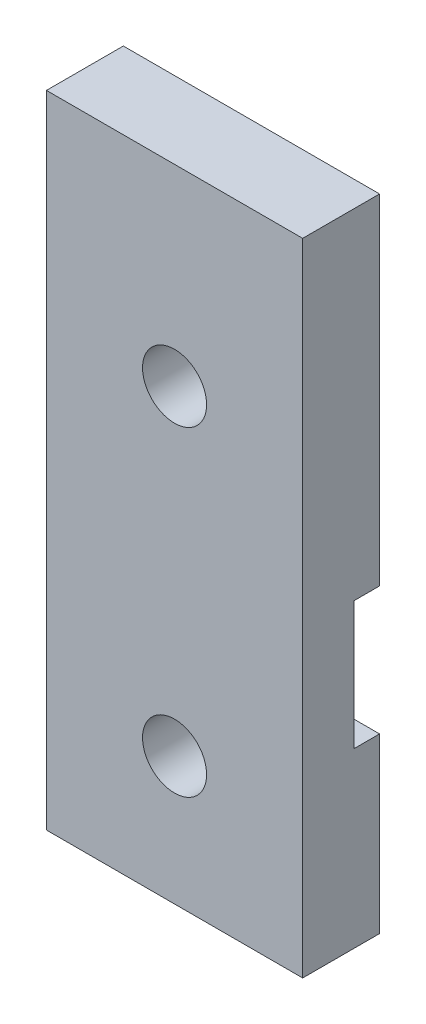
SolidWorks part; units mm, degrees
material "Policarbonato"
ref_plane "Plano frontal" through (0, 0, 0) normal (0, 0, 1) x (1, 0, 0)
ref_plane "Plano superior" through (0, 0, 0) normal (0, 1, 0) x (1, 0, 0)
ref_plane "Plano direito" through (0, 0, 0) normal (1, 0, 0) x (0, 0, -1)
sketch "Esboço1" plane through (0, 0, 0) normal (0, 0, 1) x (1, 0, 0)
  line L1 (0, 0) -> (20, 0)
  line L2 (0, 0) -> (0, 50)
  line L3 (0, 50) -> (20, 50)
  line L4 (20, 0) -> (20, 50)
  dimension "D1" = 20
  dimension "D2" = 50
extrude "Ressalto-extrusão1" add sketch "Esboço1" along normal blind 6
sketch "Esboço2" plane through (0, 0, 0) normal (0, 0, -1) x (-1, 0, 0)
  line L0 (-10, 35) -> (-10, 10) construction
  line L4 (0, 0) -> (0, 50)
  line L5 (0, 50) -> (-20, 50)
  line L6 (-20, 50) -> (-20, 0)
  line L7 (-20, 0) -> (0, 0)
  line L8 (0, 0) -> (0, 50)
  line L9 (0, 50) -> (-20, 50)
  line L10 (-20, 50) -> (-20, 0)
  line L11 (-20, 0) -> (0, 0)
  circle A0 centre (-10, 35) radius 2.5 construction
  circle A1 centre (-10, 35) radius 2.5
  circle A3 centre (-3.25, 18.5) radius 2.5 construction
  circle A5 centre (-3.25, 18.5) radius 2.5
  circle A6 centre (-10, 10) radius 2.5
  dimension "D2" = 10
  dimension "D1" = 0
extrude "Corte-extrusão1" cut sketch "Esboço2" against normal blind 10
sketch "Esboço3" plane through (0, 0, 0) normal (0, 0, 1) x (1, 0, 0)
  line L0 (10, 50) -> (10, 41.4324) construction
  line L1 (20, 50) -> (0, 50) construction
  circle A0 centre (3.25, 18.5) radius 5
  circle A1 centre (16.75, 18.5) radius 5
  dimension "D1" = 10
extrude "Corte-extrusão2" cut sketch "Esboço3" along normal blind 2
sketch "Esboço4" plane through (0, 0, 0) normal (0, 0, -1) x (-1, 0, 0)
  line L0 (-3.25, 23.5) -> (0, 23.5)
  line L1 (0, 50) -> (0, 22.2997) construction
  line L2 (0, 23.5) -> (0, 13.5)
  line L3 (0, 14.7003) -> (0, 0) construction
  line L4 (0, 13.5) -> (-3.25, 13.5)
  line L5 (-3.25, 13.5) -> (-3.25, 23.5)
  line L6 (-10, 50) -> (-10, 41.2912) construction
  line L7 (-20, 50) -> (0, 50) construction
  line L8 (-20, 13.5) -> (-16.75, 13.5)
  line L9 (-20, 23.5) -> (-20, 13.5)
  line L10 (-16.75, 23.5) -> (-20, 23.5)
  line L11 (-16.75, 13.5) -> (-16.75, 23.5)
  arc A0 (0, 22.2997) -> (0, 14.7003) centre (-3.25, 18.5) ccw construction
  arc A1 (0, 22.2997) -> (0, 14.7003) centre (-3.25, 18.5) ccw construction
  point P10 (-3.25, 18.5)
  point P15 (-3.25, 23.5)
extrude "Corte-extrusão3" cut sketch "Esboço4" against normal blind 2
sketch "Esboço5" plane through (0, 0, 6) normal (0, 0, 1) x (1, 0, 0)
  circle A0 centre (3.25, 18.5) radius 2.5 construction
  circle A1 centre (3.25, 18.5) radius 2.5
extrude "Ressalto-extrusão2" add sketch "Esboço5" against normal blind 4
